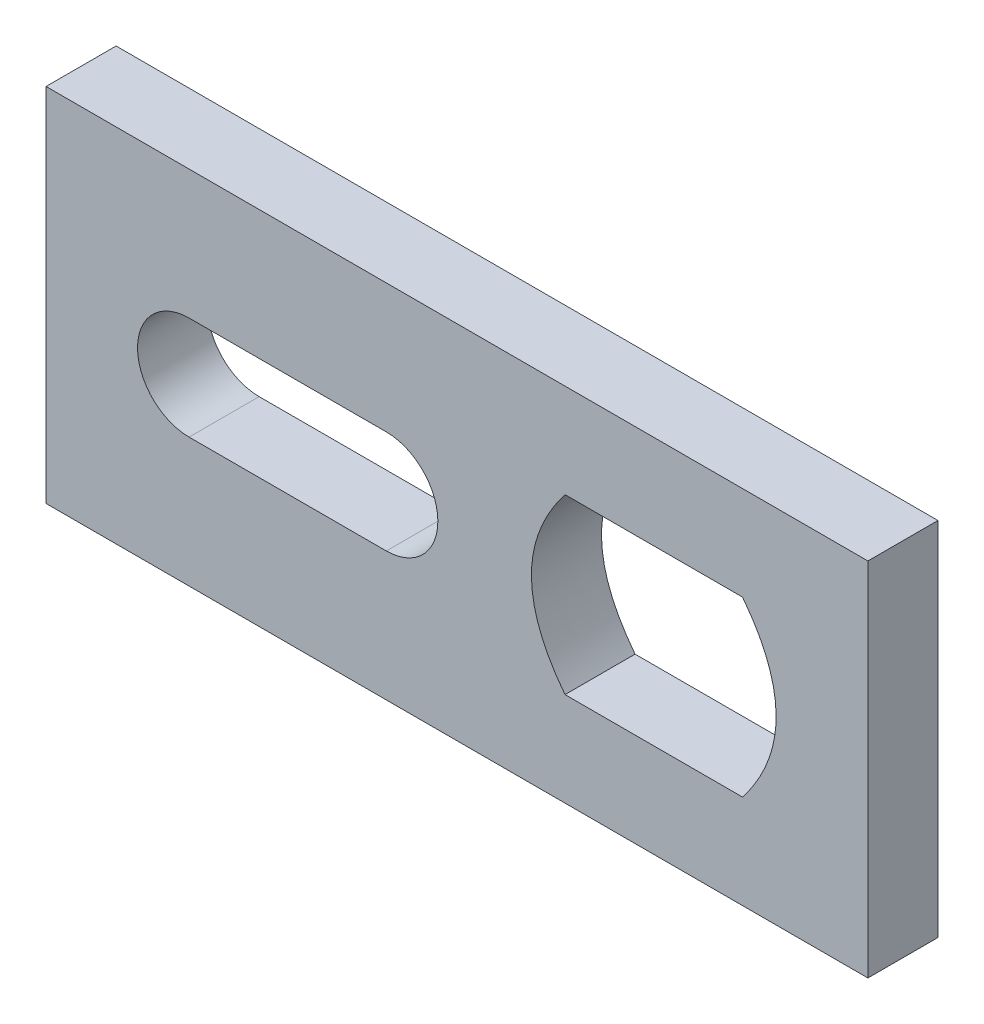
SolidWorks part; units mm, degrees
ref_plane "Front Plane" through (0, 0, 0) normal (0, 0, 1) x (1, 0, 0)
ref_plane "Top Plane" through (0, 0, 0) normal (0, 1, 0) x (1, 0, 0)
ref_plane "Right Plane" through (0, 0, 0) normal (1, 0, 0) x (0, 0, -1)
sketch "Sketch2" plane through (0, 0, 0) normal (0, 0, 1) x (1, 0, 0)
  line L0 (0, 14.975) -> (7.58, 14.975)
  line L1 (0, 0) -> (68.15, 0)
  line L2 (0, 0) -> (0, 29.95)
  line L3 (0, 29.95) -> (68.15, 29.95)
  line L4 (68.15, 0) -> (68.15, 29.95)
  line L5 (68.15, 14.975) -> (60.54, 14.975)
  line L6 (7.58, 14.975) -> (32.49, 14.975)
  line L7 (60.54, 14.975) -> (40.25, 14.975)
  line L8 (20.035, 14.975) -> (20.035, 19.25)
  line L9 (20.035, 14.975) -> (20.035, 10.7)
  line L10 (20.035, 19.25) -> (28.215, 19.25)
  line L11 (7.58, 14.975) -> (11.86, 14.975)
  line L12 (11.86, 19.25) -> (20.035, 19.25)
  line L13 (11.86, 10.7) -> (28.215, 10.7)
  line L14 (50.395, 14.975) -> (50.395, 22.155)
  line L15 (50.395, 14.975) -> (50.395, 7.795)
  line L16 (50.395, 22.155) -> (43.035, 22.155)
  line L17 (50.395, 22.155) -> (57.755, 22.155)
  line L18 (50.395, 7.795) -> (43.035, 7.795)
  line L19 (50.395, 7.795) -> (57.755, 7.795)
  circle A0 centre (28.215, 14.975) radius 4.275
  circle A1 centre (11.86, 14.975) radius 4.275
  spline S0 degree 2 poles (43.035, 7.795) (37.465, 14.975) (43.035, 22.155) knots 0 0 0 1 1 1
  spline S1 degree 2 poles (57.755, 22.155) (63.325, 14.975) (57.755, 7.795) knots 0 0 0 1 1 1
  dimension "D10" = 8.55
  dimension "D1" = 68.15
  dimension "D2" = 29.95
  dimension "D3" = 7.58
  dimension "D4" = 7.61
  dimension "D5" = 24.91
  dimension "D6" = 20.29
  dimension "D7" = 4.275
  dimension "D8" = 4.275
  dimension "D9" = 4.28
  dimension "D11" = 7.18
  dimension "D12" = 7.18
  dimension "D13" = 7.36
  dimension "D14" = 7.36
  dimension "D15" = 7.36
  dimension "D16" = 7.36
extrude "Boss-Extrude1" add sketch "Sketch2" along normal blind 5.81
